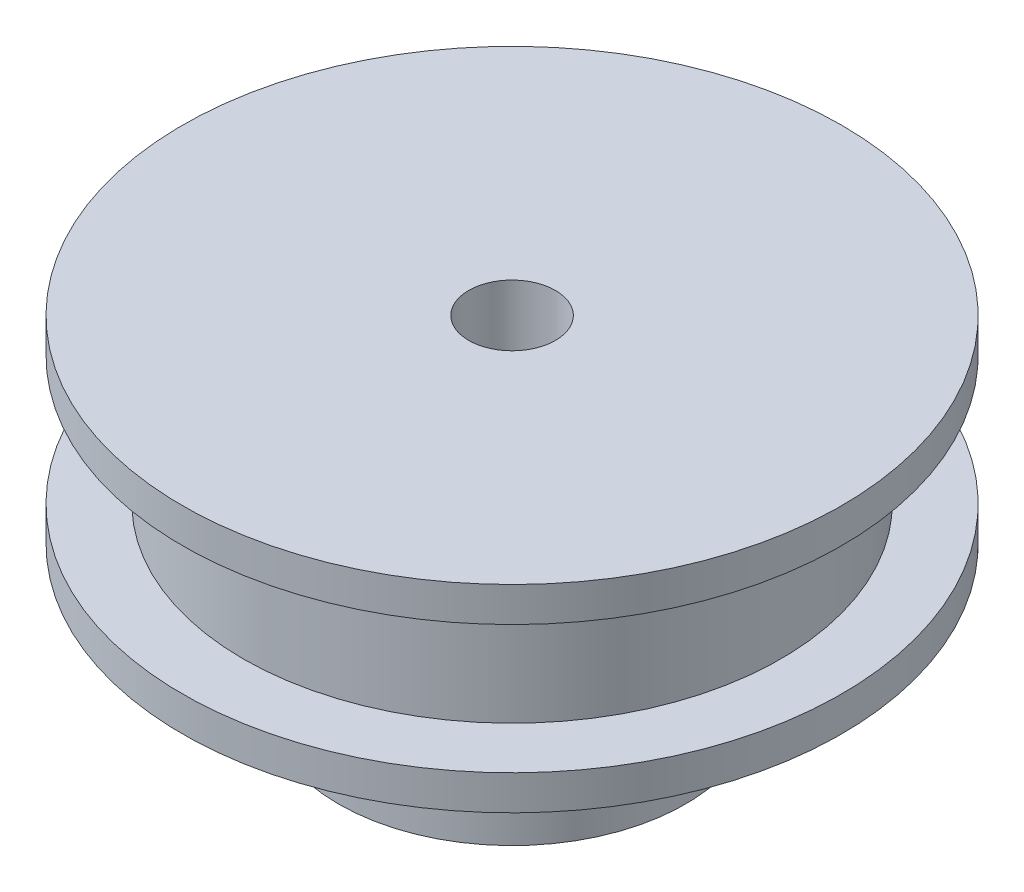
SolidWorks part; units mm, degrees
ref_plane "Спереди" through (0, 0, 0) normal (0, 0, 1) x (1, 0, 0)
ref_plane "Сверху" through (0, 0, 0) normal (0, 1, 0) x (1, 0, 0)
ref_plane "Справа" through (0, 0, 0) normal (1, 0, 0) x (0, 0, -1)
sketch "Эскиз1" plane through (0, 0, 0) normal (0, 0, 1) x (1, 0, 0)
  line L0 (0, 0) -> (0, 19.4) construction
  line L1 (-2.5, 19.4) -> (-19, 19.4)
  line L2 (-19, 19.4) -> (-19, 17.4)
  line L3 (-19, 17.4) -> (-15.5, 17.4)
  line L4 (-15.5, 17.4) -> (-15.5, 10)
  line L5 (-15.5, 10) -> (-19, 10)
  line L6 (-10, 8) -> (-10, 0)
  line L7 (-10, 0) -> (-2.5, 0)
  line L8 (-2.5, 19.4) -> (-2.5, 0)
  line L9 (-2.5, 19.4) -> (0, 19.4) construction
  line L10 (0, 0) -> (-2.5, 0) construction
  line L11 (-19, 10) -> (-19, 8)
  line L12 (-19, 8) -> (-10, 8)
  dimension "D1" = 38
  dimension "D2" = 7.4
  dimension "D3" = 2
  dimension "D4" = 8
  dimension "D5" = 5
  dimension "D6" = 31
  dimension "D7" = 20
  dimension "D8" = 2
revolve "Повернуть1" add sketch "Эскиз1" angle 360 about L0
